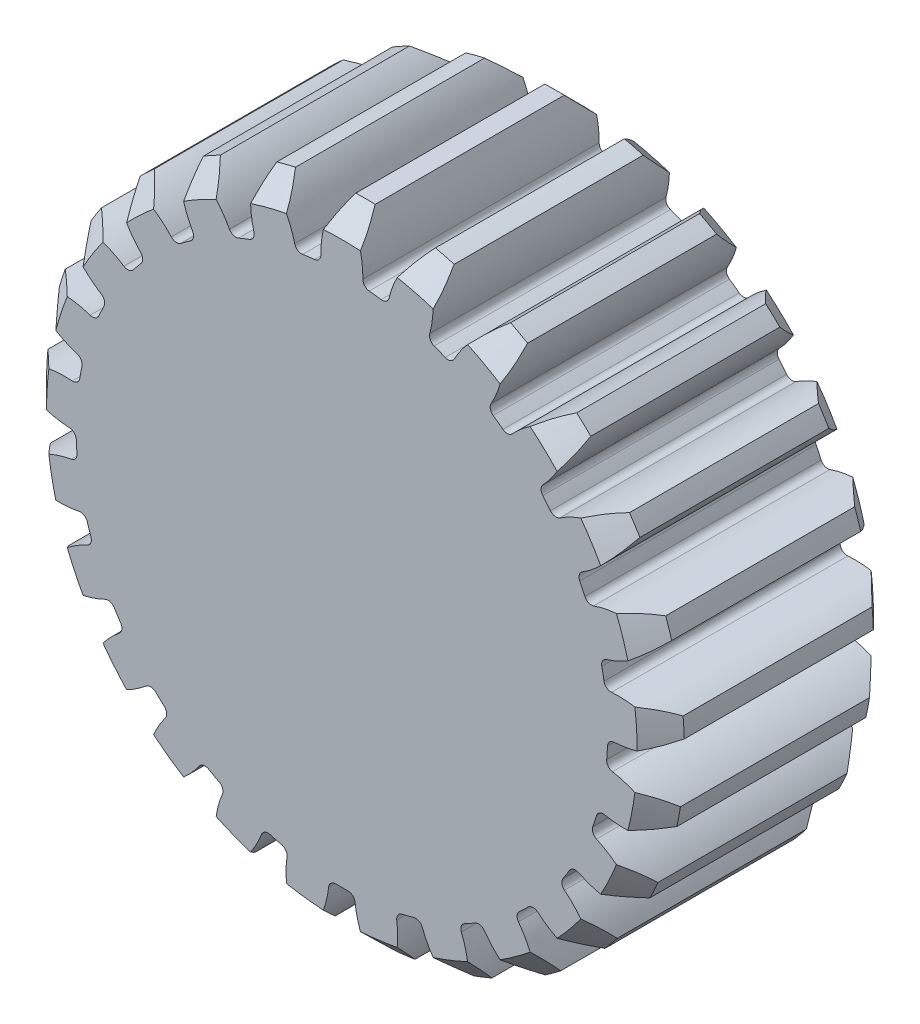
SolidWorks part; units mm, degrees
material "Plain Carbon Steel"
ref_plane "Front Plane" through (0, 0, 0) normal (0, 0, 1) x (1, 0, 0)
ref_plane "Top Plane" through (0, 0, 0) normal (0, 1, 0) x (1, 0, 0)
ref_plane "Right Plane" through (0, 0, 0) normal (1, 0, 0) x (0, 0, -1)
sketch "Sketch2" plane through (0, 0, 0) normal (0, 0, 1) x (1, 0, 0)
  circle A0 centre (0, 0) radius 25 construction
  circle A1 centre (0, 0) radius 27
  dimension "D1" = 50
  dimension "D2" = 54
extrude "Boss-Extrude1" add sketch "Sketch2" along normal mid plane 20 contours A1
sketch "Sketch3" plane through (0, 0, 0) normal (0, 0, -1) x (1, 0, 0)
  line L0 (0, 27) -> (0, 0) construction
  line L1 (0, 0) -> (3.384, 26.7871) construction
  line L2 (0, 0) -> (6.7146, 26.1517) construction
  line L3 (-1.072, 22.4744) -> (0, 0) construction
  line L4 (-1.5698, 24.9507) -> (1.5698, 24.9507) construction
  line L5 (1.5698, 24.9507) -> (4.6845, 24.5572) construction
  line L6 (-2.2805, 26.9035) -> (0, 20.6378) construction
  circle A0 centre (0, 0) radius 23 construction
  arc A1 (1.072, 22.4744) -> (-1.072, 22.4744) centre (0, 0) ccw
  circle A2 centre (0, 0) radius 27 construction
  arc A4 (-2.5691, 26.8775) -> (-1.072, 22.4744) centre (-9.4743, 22.0737) cw
  circle A5 centre (0, 0) radius 27 construction
  arc A6 (2.5691, 26.8775) -> (1.072, 22.4744) centre (9.4743, 22.0737) ccw
  circle A7 centre (0, 0) radius 25 construction
  arc A8 (-2.5691, 26.8775) -> (2.5691, 26.8775) centre (0, 0) cw
  dimension "D1" = 14.4
  dimension "D2" = 4
  dimension "D3" = 4.5
  dimension "D4" = 0.5
  dimension "D5" = 20
extrude "Cut-Extrude1" cut sketch "Sketch3" against normal through all both and the other way through all
fillet "Fillet1" radius 0.6 2 edges at (-1.072, -22.4744, 0) (1.072, -22.4744, 0)
chamfer "Chamfer1" distance 2 2 edges at (0, 27, 10) (0, 27, -10)
pattern_circular "CirPattern1" count 25 over 360 about axis through (0, 0, 0) along (0, 0, 1) of "Cut-Extrude1", "Fillet1"
equation "\"Module\"= 2mm"
equation "\"Number of teeth\"= 25"
equation "\"Pressure Angle\"= 20"
equation "\"D1@Sketch2\"=\"Module\" * \"Number of teeth\""
equation "\"D2@Sketch2\"=(\"Number of teeth\" + 2) *\"Module\""
equation "\"D1@Sketch3\"= 360/ \"Number of teeth\""
equation "\"D2@Sketch3\"= \"Module\" * 2"
equation "\"D3@Sketch3\"= \"Module\" * if( \"Module\" => 1.25, 2.25, 2.4)"
equation "\"D5@Sketch3\"=\"Pressure Angle\""
equation "\"D1@Chamfer1\"= \"Module\""
equation "\"D1@CirPattern1\"= \"Number of teeth\""
